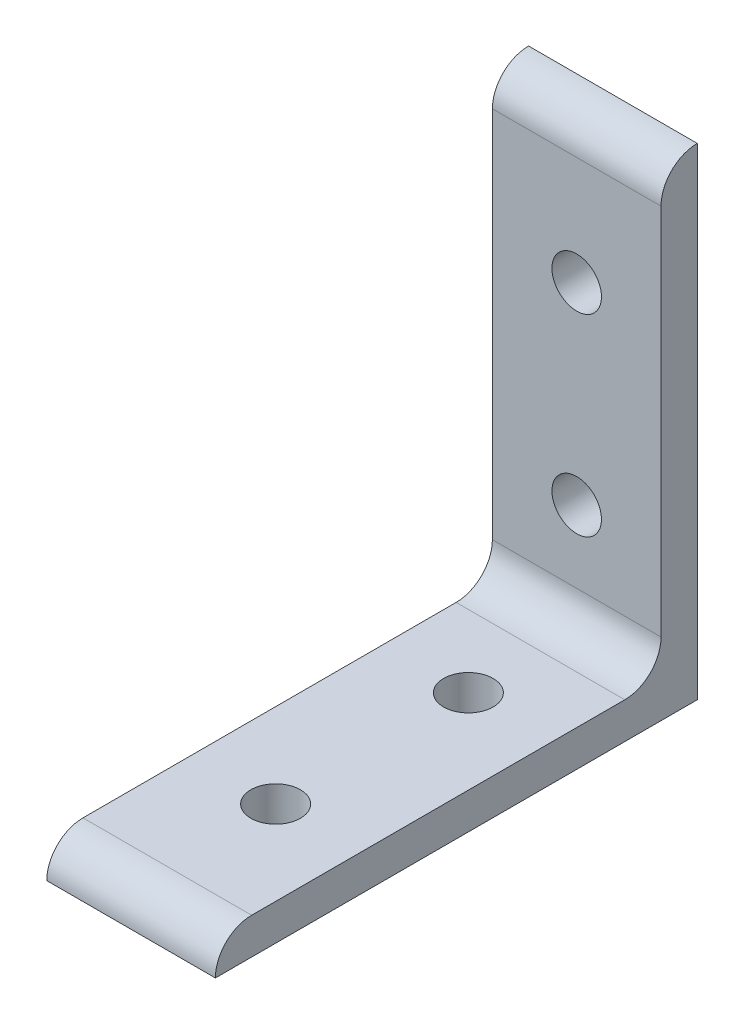
SolidWorks part; units mm, degrees
material "6061 Alloy"
ref_plane "Front Plane" through (0, 0, 0) normal (0, 0, 1) x (1, 0, 0)
ref_plane "Top Plane" through (0, 0, 0) normal (0, 1, 0) x (1, 0, 0)
ref_plane "Right Plane" through (0, 0, 0) normal (1, 0, 0) x (0, 0, -1)
sketch "Sketch1" plane through (0, 0, 0) normal (1, 0, 0) x (0, 0, -1)
  line L0 (23.9708, -29.6061) -> (19.1956, -24.8309)
  line L1 (23.9708, -29.6061) -> (-39.5292, -29.6061)
  line L2 (19.1956, -24.8309) -> (-34.754, -24.8309)
  line L3 (23.9708, -24.8309) -> (-39.5292, -24.8309) construction
  arc A0 (-34.754, -24.8309) -> (-39.5292, -29.6061) centre (-34.754, -29.6061) ccw
  dimension "D1" = 63.5
  dimension "D2" = 4.7752
extrude "Extrude1" add sketch "Sketch1" along normal blind 22.225
sketch "Sketch2" plane through (0, -24.8309, 0) normal (0, 1, 0) x (1, 0, 0)
  circle A0 centre (11.1125, -20.4792) radius 3.2639
  circle A1 centre (11.1125, 4.9208) radius 3.2639
extrude "Cut-Extrude1" cut sketch "Sketch2" against normal blind 22.225
mirror "Mirror1" about plane through (22.225, -29.6061, -23.9708) normal (0, -0.7071, 0.7071) of bodies 102
fillet "Fillet1" radius 4.7752 1 edges at (11.1125, -24.8309, -19.1956)
